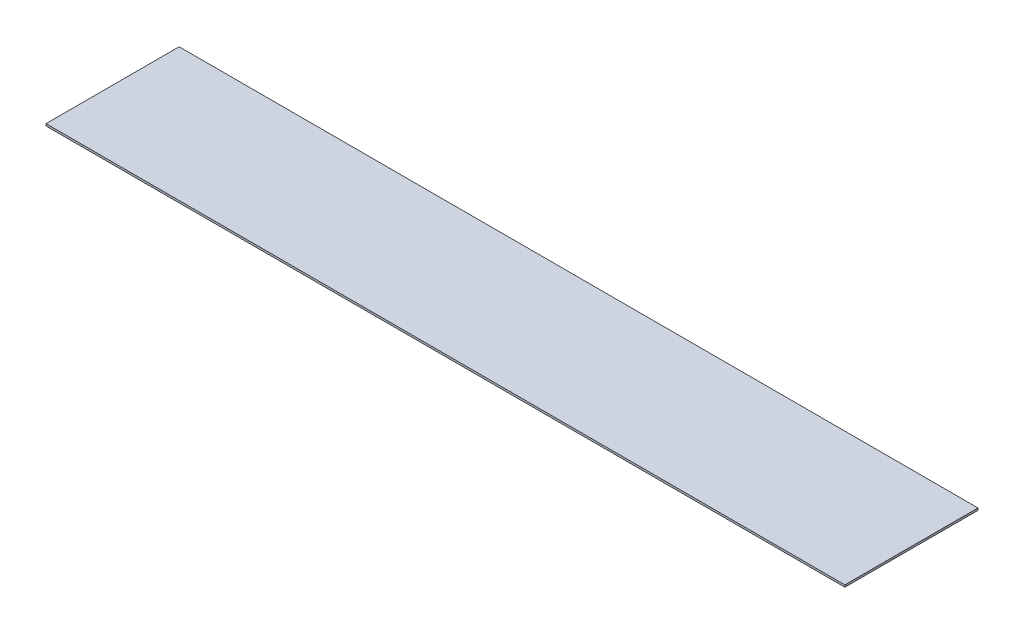
SolidWorks part; units mm, degrees
material "Nylon 101"
ref_plane "Front Plane" through (0, 0, 0) normal (0, 0, 1) x (1, 0, 0)
ref_plane "Top Plane" through (0, 0, 0) normal (0, 1, 0) x (1, 0, 0)
ref_plane "Right Plane" through (0, 0, 0) normal (1, 0, 0) x (0, 0, -1)
sketch "Sketch1" plane through (0, 0, 0) normal (0, -1, 0) x (1, 0, 0)
  line L2 (0, 0) -> (609.6, 0)
  line L3 (0, 0) -> (0, 101.6)
  line L4 (0, 101.6) -> (609.6, 101.6)
  line L5 (609.6, 0) -> (609.6, 101.6)
  dimension "D2" = 609.6
  dimension "D1" = 101.6
extrude "Boss-Extrude1" add sketch "Sketch1" along normal blind 1.5875
